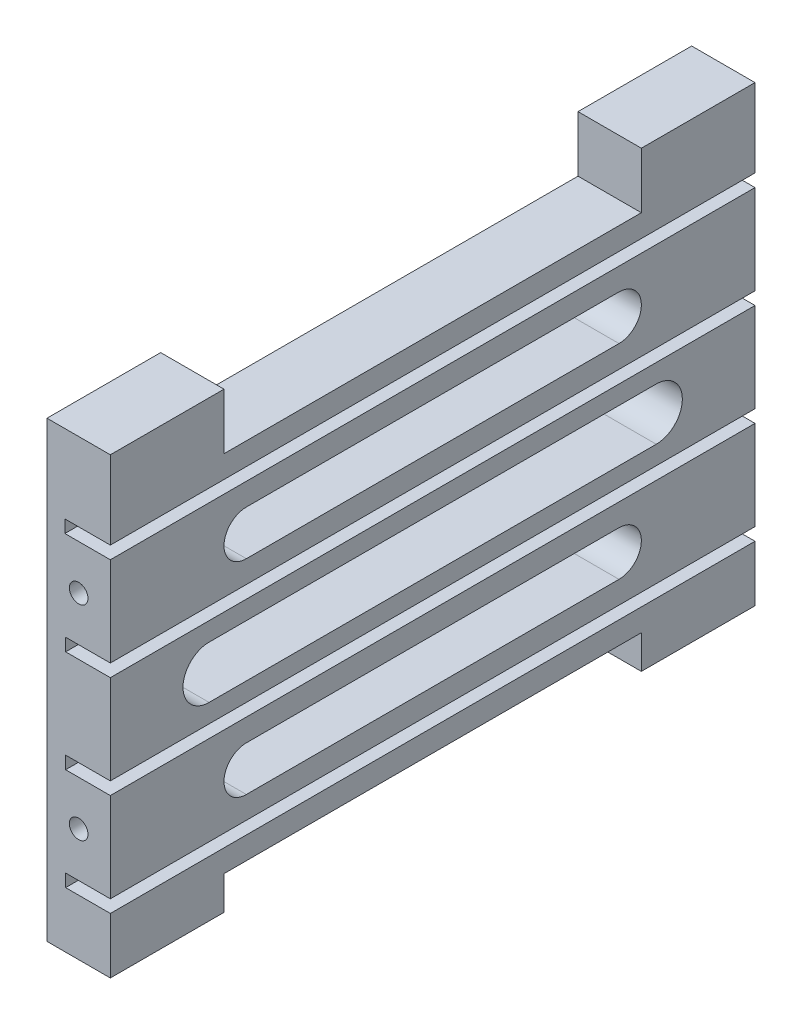
SolidWorks part; units mm, degrees
material "6061-T6 (SS)"
ref_plane "Front Plane" through (0, 0, 0) normal (0, 0, 1) x (1, 0, 0)
ref_plane "Top Plane" through (0, 0, 0) normal (0, 1, 0) x (1, 0, 0)
ref_plane "Right Plane" through (0, 0, 0) normal (1, 0, 0) x (0, 0, -1)
sketch "Sketch1" plane through (0, 0, 0) normal (0, 0, 1) x (1, 0, 0)
  line L0 (0, 0) -> (0, 60.8)
  line L1 (0, 60.8) -> (8.5, 60.8)
  line L2 (8.5, 60.8) -> (8.5, 50.3)
  line L3 (8.5, 50.3) -> (2.4, 50.3)
  line L4 (2.4, 50.3) -> (2.4, 48.6)
  line L5 (2.4, 48.6) -> (8.5, 48.6)
  line L6 (8.5, 48.6) -> (8.5, 36.6)
  line L7 (8.5, 36.6) -> (2.5, 36.6)
  line L8 (2.5, 36.6) -> (2.5, 34.9)
  line L9 (2.5, 34.9) -> (8.5, 34.9)
  line L10 (8.5, 34.9) -> (8.5, 22.9)
  line L11 (8.5, 22.9) -> (2.5, 22.9)
  line L12 (2.5, 22.9) -> (2.5, 21.2)
  line L13 (2.5, 21.2) -> (8.5, 21.2)
  line L14 (8.5, 21.2) -> (8.5, 9.2)
  line L15 (8.5, 9.2) -> (2.5, 9.2)
  line L16 (2.5, 9.2) -> (2.5, 7.5)
  line L17 (2.5, 7.5) -> (8.5, 7.5)
  line L18 (8.5, 7.5) -> (8.5, 0)
  line L19 (8.5, 0) -> (0, 0)
  dimension "D1" = 60.8
  dimension "D2" = 8.5
  dimension "D3" = 10.5
  dimension "D4" = 1.7
  dimension "D5" = 6.1
  dimension "D6" = 12
  dimension "D7" = 1.7
  dimension "D8" = 12
  dimension "D9" = 12
  dimension "D10" = 1.7
  dimension "D11" = 1.7
  dimension "D12" = 2.5
  dimension "D13" = 2.5
  dimension "D14" = 2.5
  dimension "D15" = 8.5
  dimension "D16" = 8.5
  dimension "D17" = 8.5
  dimension "D18" = 8.5
extrude "Boss-Extrude1" add sketch "Sketch1" along normal blind 86.5
sketch "Sketch2" plane through (0, 0, 86.5) normal (0, 0, 1) x (1, 0, 0)
  line L0 (8.5, 36.6) -> (8.5, 48.6) construction
  line L3 (8.5, 48.6) -> (2.4, 48.6) construction
  line L4 (8.5, 21.2) -> (2.5, 21.2) construction
  line L8 (8.5, 9.2) -> (8.5, 21.2) construction
  point P0 (4.25, 15.2)
  point P11 (4.25, 42.6)
  dimension "D1" = 4.25
  dimension "D2" = 6
  dimension "D3" = 4.25
  dimension "D4" = 6
hole_wizard "M3x0.5 Tapped Hole2" positions "Sketch3" profile "Sketch4" tap size "M3x0.5" standard "ANSI Metric"
sketch "Sketch3" plane through (0, 0, 86.5) normal (0, 0, 1) x (1, 0, 0)
  point P0 (4.25, 42.6)
  point P3 (4.25, 15.2)
sketch "Sketch4" plane through (4.25, 42.6, 86.5) normal (1, 0, 0) x (0, -1, 0)
  line L0 (0, 0) -> (0, 6.7511)
  line L1 (0, 6.7511) -> (1.25, 6)
  line L2 (1.25, 6) -> (1.25, 0)
  line L5 (1.25, 0) -> (0, 0)
  line L10 (0, 6.7511) -> (-1.25, 6) construction
  line L11 (0, -6.35) -> (0, 107.95) construction
  dimension "Tap Drill Dia." = 2.5
  dimension "Tap Drill Depth" = 6
  dimension "Drill Angle" = 118
ref_plane "Plane1" through (0, 0, 43.25) normal (0, 0, 1) x (1, 0, 0)
mirror "Mirror1" about plane through (0, 0, 43.25) normal (0, 0, 1) of "M3x0.5 Tapped Hole2"
sketch "Sketch5" plane through (0, 0, 0) normal (-1, 0, 0) x (0, 0, 1)
  line L1 (86.5, 60.8) -> (0, 60.8) construction
  line L5 (0, 60.8) -> (0, 0) construction
  line L7 (86.5, 0) -> (0, 0) construction
  line L8 (86.5, 60.8) -> (86.5, 0) construction
  point P0 (78.25, 5)
  point P3 (8.25, 5)
  point P4 (8.25, 55.8)
  point P7 (78.25, 55.8)
  dimension "D1" = 5
  dimension "D2" = 8.25
  dimension "D3" = 70
  dimension "D4" = 5
  dimension "D5" = 5
  dimension "D6" = 8.25
  dimension "D7" = 8.25
  dimension "D8" = 5
hole_wizard "M3x0.5 Tapped Hole1" positions "Sketch10" profile "Sketch11" tap size "M3x0.5" standard "ANSI Metric"
sketch "Sketch10" plane through (0, 0, 0) normal (-1, 0, 0) x (0, 0, 1)
  line L0 (43.25, 60.8) -> (43.25, 0) construction
  line L1 (86.5, 60.8) -> (0, 60.8) construction
  line L2 (86.5, 0) -> (0, 0) construction
  line L7 (43.25, 54) -> (8.25, 54) construction
  line L12 (43.25, 5) -> (8.25, 5) construction
  point P16 (8.25, 54)
  point P26 (8.25, 5)
  dimension "D1" = 49
sketch "Sketch11" plane through (0, 5, 8.25) normal (0, 1, 0) x (0, 0, 1)
  line L0 (0, 0) -> (0, 4.7511)
  line L1 (0, 4.7511) -> (1.25, 4)
  line L2 (1.25, 4) -> (1.25, 0)
  line L5 (1.25, 0) -> (0, 0)
  line L10 (0, 4.7511) -> (-1.25, 4) construction
  line L11 (0, -6.35) -> (0, 107.95) construction
  dimension "Tap Drill Dia." = 2.5
  dimension "Tap Drill Depth" = 4
  dimension "Drill Angle" = 118
ref_plane "Plane2" through (0, 0, 43.25) normal (0, 0, -1) x (-1, 0, 0)
mirror "Mirror2" about plane through (0, 0, 43.25) normal (0, 0, -1) of "M3x0.5 Tapped Hole1"
sketch "Sketch14" plane through (8.5, 0, 0) normal (1, 0, 0) x (0, 0, -1)
  line L0 (-43.25, 60.8) -> (-43.25, 0) construction
  line L1 (-86.5, 60.8) -> (0, 60.8) construction
  line L2 (-86.5, 0) -> (0, 0) construction
  line L3 (-86.5, 28.9) -> (0, 28.9) construction
  line L4 (-86.5, 22.9) -> (-86.5, 34.9) construction
  line L5 (0, 22.9) -> (0, 34.9) construction
  line L6 (-73.25, 32.4) -> (-13.25, 32.4)
  line L7 (-13.25, 25.4) -> (-73.25, 25.4)
  circle A0 centre (-73.25, 28.9) radius 3.5
  circle A1 centre (-13.25, 28.9) radius 3.5
  dimension "D1" = 7
  dimension "D2" = 30
extrude "Cut-Extrude3" cut sketch "Sketch14" against normal through all contours A1 L6 A0 L7 | A0 | A1
sketch "Sketch12" plane through (8.5, 0, 0) normal (1, 0, 0) x (0, 0, -1)
  line L0 (-43.25, 60.8) -> (-43.25, 0) construction
  line L1 (-86.5, 60.8) -> (0, 60.8) construction
  line L2 (-86.5, 0) -> (0, 0) construction
  line L3 (-86.5, 21.2) -> (0, 21.2) construction
  line L4 (-68.25, 45.6) -> (-18.25, 45.6)
  line L5 (-68.25, 39.6) -> (-18.25, 39.6)
  line L6 (-68.25, 18.2) -> (-18.25, 18.2)
  line L7 (-68.25, 12.2) -> (-18.25, 12.2)
  line L9 (-86.5, 48.6) -> (0, 48.6) construction
  circle A0 centre (-68.25, 42.6) radius 3
  circle A1 centre (-18.25, 42.6) radius 3
  circle A2 centre (-18.25, 15.2) radius 3
  circle A3 centre (-68.25, 15.2) radius 3
  dimension "D1" = 6
  dimension "D2" = 25
  dimension "D3" = 3
  dimension "D4" = 3
extrude "Cut-Extrude1" cut sketch "Sketch12" against normal through all contours A0 | A3 | A2 | A1 | L0 L6 A3 L7 | L6 L0 L7 A2 | L4 L0 L5 A1 | L0 L4 A0 L5
sketch "Sketch15" plane through (8.5, 0, 0) normal (1, 0, 0) x (0, 0, -1)
  line L0 (-86.5, 60.8) -> (0, 60.8) construction
  line L1 (-71.25, 60.8) -> (-15.25, 60.8)
  line L2 (-71.25, 60.8) -> (-71.25, 53.3)
  line L3 (-71.25, 53.3) -> (-15.25, 53.3)
  line L4 (-15.25, 60.8) -> (-15.25, 53.3)
  line L5 (-71.25, 60.8) -> (-15.25, 53.3) construction
  line L6 (-71.25, 53.3) -> (-15.25, 60.8) construction
  point P0 (-43.25, 57.05)
  point P7 (-43.25, 60.8)
  dimension "D1" = 56
  dimension "D2" = 7.5
extrude "Cut-Extrude4" cut sketch "Sketch15" against normal through all contours L2 L3 L4 L1
sketch "Sketch16" plane through (8.5, 0, 0) normal (1, 0, 0) x (0, 0, -1)
  line L0 (-86.5, 0) -> (0, 0) construction
  line L1 (-71.25, 4.5) -> (-15.25, 4.5)
  line L2 (-71.25, 4.5) -> (-71.25, 0)
  line L3 (-71.25, 0) -> (-15.25, 0)
  line L4 (-15.25, 4.5) -> (-15.25, 0)
  line L5 (-71.25, 4.5) -> (-15.25, 0) construction
  line L6 (-71.25, 0) -> (-15.25, 4.5) construction
  point P0 (-43.25, 2.25)
  point P5 (0, 0)
  point P8 (-43.25, 0)
  dimension "D1" = 4.5
  dimension "D2" = 56
extrude "Cut-Extrude5" cut sketch "Sketch16" against normal through all
